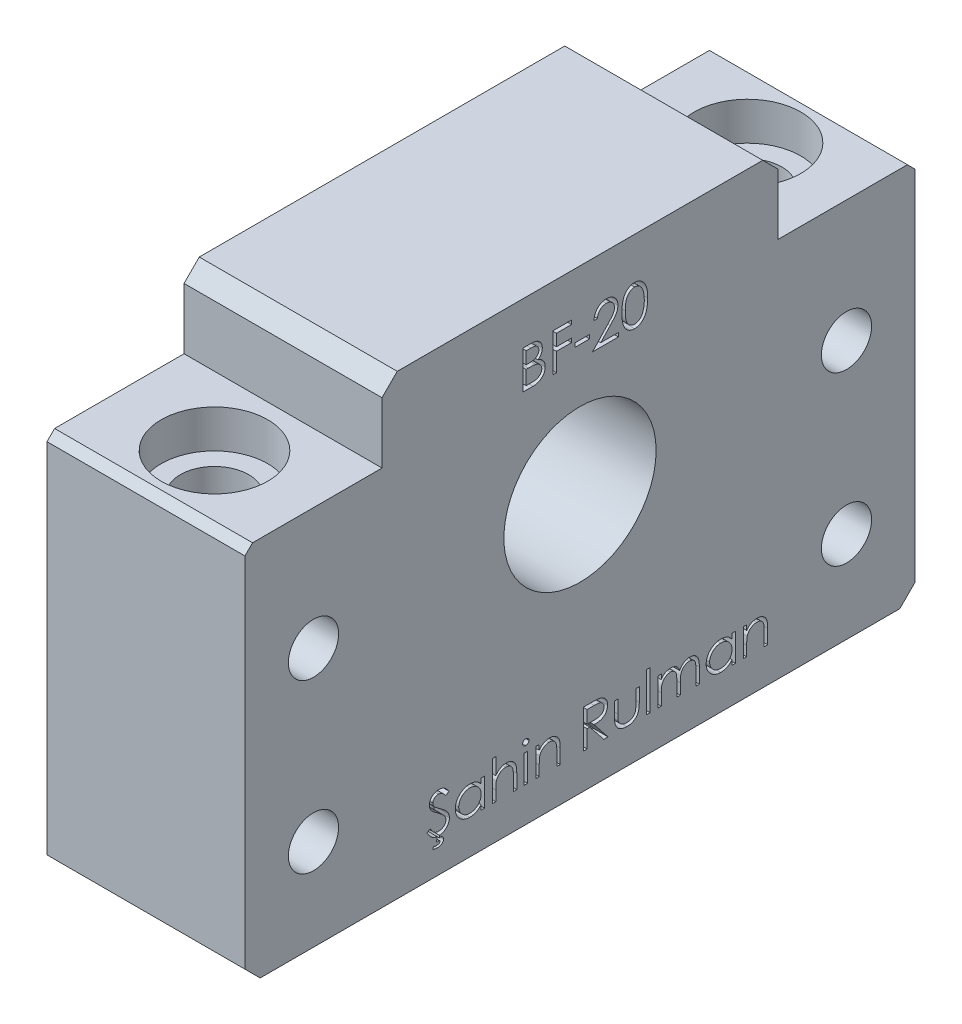
SolidWorks part; units mm, degrees
ref_plane "Front Plane" through (0, 0, 0) normal (0, 0, 1) x (1, 0, 0)
ref_plane "Top Plane" through (0, 0, 0) normal (0, 1, 0) x (1, 0, 0)
ref_plane "Right Plane" through (0, 0, 0) normal (1, 0, 0) x (0, 0, -1)
sketch "Sketch1" plane through (0, 0, 0) normal (1, 0, 0) x (0, 0, -1)
  line L0 (-44, 0) -> (44, 0)
  line L1 (44, 0) -> (44, 50)
  line L2 (44, 50) -> (26, 50)
  line L3 (26, 50) -> (26, 60)
  line L4 (26, 60) -> (-26, 60)
  line L5 (-26, 60) -> (-26, 50)
  line L6 (-26, 50) -> (-44, 50)
  line L7 (-44, 50) -> (-44, 0)
  line L8 (0, -19.956) -> (0, 74.2362) construction
  circle A0 centre (0, 34) radius 10
  dimension "D8" = 20
  dimension "D1" = 52
  dimension "D2" = 26
  dimension "D3" = 88
  dimension "D4" = 44
  dimension "D5" = 60
  dimension "D6" = 50
  dimension "D7" = 50
  dimension "D9" = 34
extrude "Boss-Extrude1" add sketch "Sketch1" along normal mid plane 26
chamfer "Chamfer1" distance 2 angle 45 4 edges at (0, 0, -44) (0, 0, 44) (0, 60, -26) (0, 60, 26)
chamfer "Chamfer2" distance 1 angle 45 2 edges at (0, 50, -44) (0, 50, 44)
sketch "Sketch2" plane through (0, 50, 0) normal (0, 1, 0) x (1, 0, 0)
  line L0 (0, -48.8038) -> (0, 46.6348) construction
  circle A0 centre (0, 35) radius 7
  circle A1 centre (0, -35) radius 7
  dimension "D3" = 14
  dimension "D4" = 14
extrude "Cut-Extrude1" cut sketch "Sketch2" against normal blind 5
sketch "Sketch3" plane through (0, 45, 0) normal (0, 1, 0) x (1, 0, 0)
  circle A0 centre (0, -35) radius 4.5
  circle A1 centre (0, 35) radius 4.5
  dimension "D1" = 9
  dimension "D2" = 9
extrude "Cut-Extrude2" cut sketch "Sketch3" against normal through all
sketch "Sketch4" plane through (13, 0, 0) normal (1, 0, 0) x (0, 0, -1)
  circle A0 centre (-35, 34) radius 3.3
  circle A1 centre (-35, 12) radius 3.3
  circle A2 centre (35, 12) radius 3.3
  circle A3 centre (35, 34) radius 3.3
  dimension "D1" = 6.6
  dimension "D3" = 6.6
  dimension "D2" = 35
  dimension "D4" = 70
  dimension "D5" = 70
  dimension "D6" = 35
extrude "Cut-Extrude13" cut sketch "Sketch4" against normal blind 6.6
sketch "Sketch5" plane through (13, 0, 0) normal (1, 0, 0) x (0, 0, -1)
  text T0 "Şahin Rulman" font "Century Gothic" height 5
extrude "Cut-Extrude14" cut sketch "Sketch5" against normal blind 2
sketch "Sketch6" plane through (13, 0, 0) normal (1, 0, 0) x (0, 0, -1)
  text T0 "BF-20" font "Century Gothic" height 5
extrude "Cut-Extrude15" cut sketch "Sketch6" against normal blind 2
